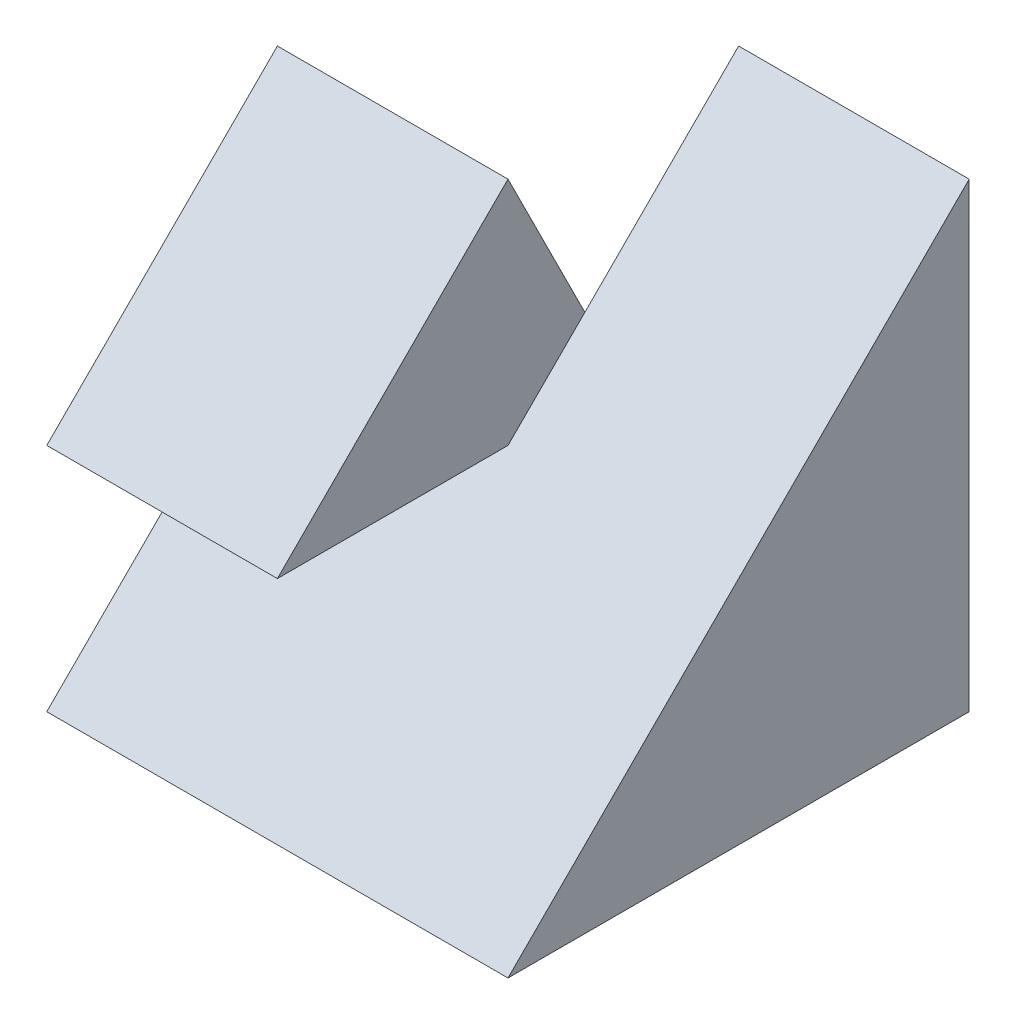
SolidWorks part; units mm, degrees
ref_plane "Front" through (0, 0, 0) normal (0, 0, 1) x (1, 0, 0)
ref_plane "Top" through (0, 0, 0) normal (0, 1, 0) x (1, 0, 0)
ref_plane "Right" through (0, 0, 0) normal (1, 0, 0) x (0, 0, -1)
sketch "Sketch1" plane through (0, 0, 0) normal (0, 1, 0) x (1, 0, 0)
  line L1 (-2, -2) -> (2, -2)
  line L2 (-2, -2) -> (-2, 2)
  line L3 (-2, 2) -> (2, 2)
  line L4 (2, -2) -> (2, 2)
  line L5 (-2, -2) -> (2, 2) construction
  line L6 (-2, 2) -> (2, -2) construction
  point P0 (0, 0)
  dimension "D1" = 4
  dimension "D2" = 4
extrude "Boss-Extrude1" add sketch "Sketch1" along normal blind 4
sketch "Sketch2" plane through (-2, 0, 0) normal (-1, 0, 0) x (0, 0, 1)
  line L0 (2, 0) -> (0, 2)
  line L1 (0, 2) -> (2, 2)
  line L2 (2, 4) -> (2, 0) construction
  line L3 (2, 2) -> (0, 4)
  line L4 (-2, 4) -> (2, 4) construction
  line L5 (0, 4) -> (2, 4)
  line L6 (2, 4) -> (2, 0)
  line L8 (-2, 4) -> (-2, 0) construction
  line L9 (-2, 2) -> (-2, 4)
  line L10 (-2, 4) -> (0, 4)
  line L11 (0, 4) -> (-2, 0)
  line M2 (2, 0) -> (2, 4)
  line M3 (2, 4) -> (-2, 4)
  line M4 (-2, 4) -> (-2, 0)
extrude "Cut-Extrude1" cut sketch "Sketch2" against normal blind 2 contours L1 L0 M2 | L3 M2 M3 | L11 M3 M4
sketch "Sketch3" plane through (2, 0, 0) normal (1, 0, 0) x (0, 0, -1)
  line L0 (-2, 0) -> (2, 4)
  line L1 (2, 4) -> (-2, 4.1166)
  line L2 (-2, 4.1166) -> (-2, 0)
extrude "Cut-Extrude2" cut sketch "Sketch3" against normal blind 2
